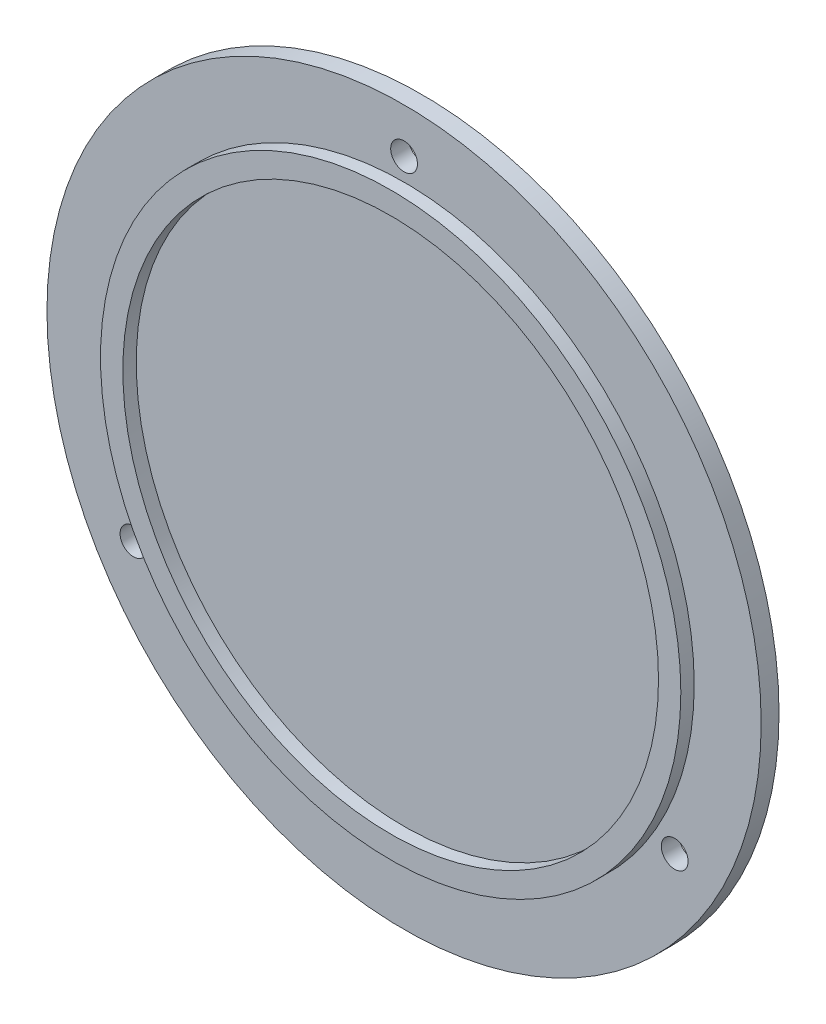
SolidWorks part; units mm, degrees
ref_plane "Front Plane" through (0, 0, 0) normal (0, 0, 1) x (1, 0, 0)
ref_plane "Top Plane" through (0, 0, 0) normal (0, 1, 0) x (1, 0, 0)
ref_plane "Right Plane" through (0, 0, 0) normal (1, 0, 0) x (0, 0, -1)
sketch "Sketch1" plane through (0, 0, 0) normal (0, 0, 1) x (1, 0, 0)
  circle A0 centre (0, 0) radius 80
extrude "Boss-Extrude1" add sketch "Sketch1" along normal blind 4
sketch "Sketch2" plane through (0, 0, 4) normal (0, 0, 1) x (1, 0, 0)
  circle A0 centre (0, 0) radius 65
  circle A1 centre (0, 0) radius 60
extrude "Boss-Extrude2" add sketch "Sketch2" along normal blind 3
sketch "Sketch3" plane through (0, 0, 0) normal (0, 0, -1) x (-1, 0, 0)
  circle A0 centre (0, 0) radius 70
  circle A1 centre (0, 70) radius 3
  circle A2 centre (60.6218, -35) radius 3
  circle A3 centre (-60.6218, -35) radius 3
  point P11 (0, 0)
  dimension "D1" = 3
extrude "Cut-Extrude2" cut sketch "Sketch3" against normal through all contours A1 | A3 | A2
